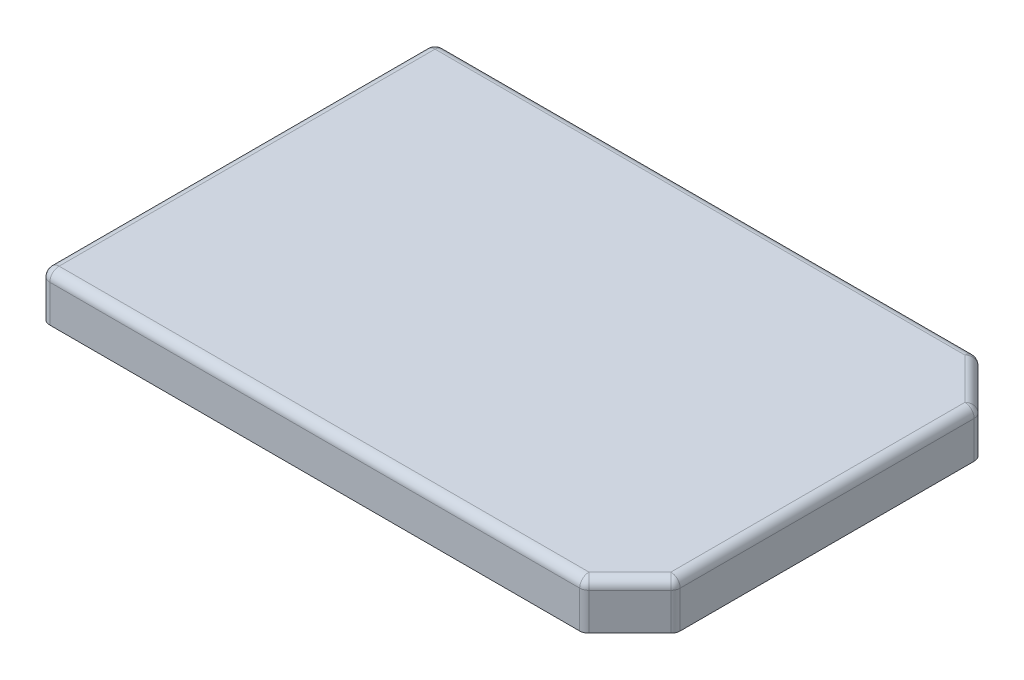
SolidWorks part; units mm, degrees
ref_plane "Front Plane" through (0, 0, 0) normal (0, 0, 1) x (1, 0, 0)
ref_plane "Top Plane" through (0, 0, 0) normal (0, 1, 0) x (1, 0, 0)
ref_plane "Right Plane" through (0, 0, 0) normal (1, 0, 0) x (0, 0, -1)
sketch "Sketch1" plane through (0, 0, 0) normal (0, 1, 0) x (1, 0, 0)
  line L1 (0, 0) -> (127, 0)
  line L2 (0, 0) -> (0, -85)
  line L3 (0, -85) -> (127, -85)
  line L4 (127, 0) -> (127, -85)
  dimension "D1" = 127
  dimension "D2" = 85
extrude "Boss-Extrude1" add sketch "Sketch1" along normal blind 10
chamfer "Chamfer1" distance 10 angle 45 2 edges at (127, 5, 0) (127, 5, 85)
fillet "Fillet1" radius 2 6 edges at (117, 5, 0) (127, 5, 10) (0, 5, 85) (0, 5, 0) (127, 5, 75) (117, 5, 85)
fillet "Fillet2" radius 2 12 edges at (59.0858, 10, 0) (116.9369, 10, 0.1522) (122, 10, 5) (126.8478, 10, 10.0631) (127, 10, 42.5) (59.0858, 10, 85) (0, 10, 42.5) (0.5858, 10, 84.4142) (0.5858, 10, 0.5858) (126.8478, 10, 74.9369) (122, 10, 80) (116.9369, 10, 84.8478)
sketch "Sketch2" plane through (0, 0, 0) normal (0, -1, 0) x (1, 0, 0)
  line L1 (1.25, 83.75) -> (115.75, 83.75)
  line L2 (1.25, 83.75) -> (1.25, 1.25)
  line L3 (1.25, 1.25) -> (115.75, 1.25)
  line L4 (125.75, 73.75) -> (125.75, 11.25)
  line L5 (0, 2) -> (0, 83) construction
  line L6 (115.75, 1.25) -> (125.75, 11.25)
  line L7 (115.75, 83.75) -> (125.75, 73.75)
  line L8 (125.75, 42.5) -> (1.25, 42.5) construction
  line L9 (127, 63.0027) -> (0, 63.0027) construction
  line L10 (127, 74.1716) -> (127, 10.8284) construction
  line L11 (0, 2) -> (0, 83) construction
  point P1 (125.75, 1.25)
  point P3 (125.75, 83.75)
  point P9 (1.25, 42.5)
  point P12 (0, 42.5)
  point P24 (63.5, 63.0027)
  point P25 (63.5, 42.5)
  point P26 (1.2621, 42.5)
  dimension "D1" = 124.5
  dimension "D2" = 82.5
extrude "Cut-Extrude1" cut sketch "Sketch2" against normal blind 7.3
